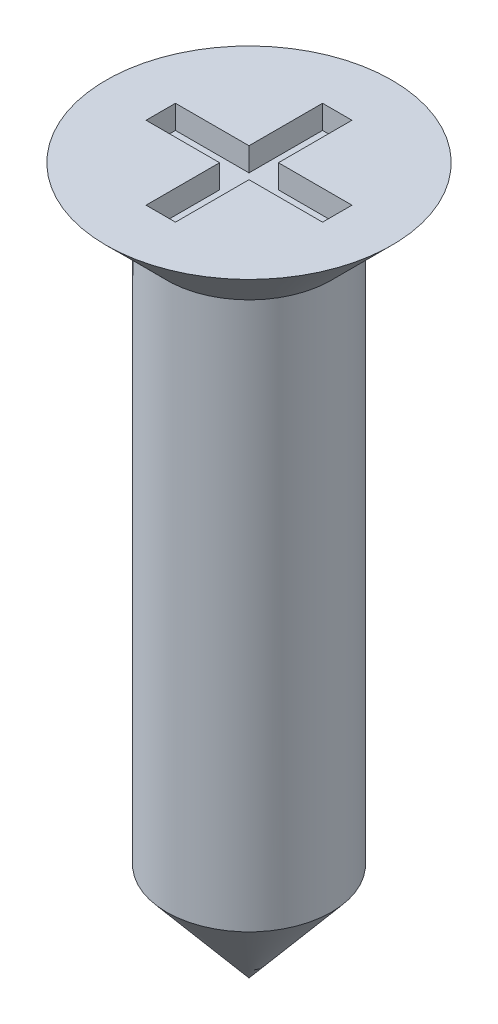
SolidWorks part; units mm, degrees
ref_plane "Front" through (0, 0, 0) normal (0, 0, 1) x (1, 0, 0)
ref_plane "Top" through (0, 0, 0) normal (0, 1, 0) x (1, 0, 0)
ref_plane "Right" through (0, 0, 0) normal (1, 0, 0) x (0, 0, -1)
sketch "Sketch1" plane through (0, 0, 0) normal (0, 0, 1) x (1, 0, 0)
  line L0 (0, 0) -> (-1.215, 0)
  line L1 (-1.215, 0) -> (-0.7, -0.515)
  line L2 (-0.7, -0.515) -> (-0.7, -5.1658)
  line L3 (-0.7, -5.1658) -> (0, -6)
  line L4 (0, -6) -> (0, 0) construction
  line L5 (0, 0) -> (0, -6)
  line L6 (0, -6) -> (-0.7, -6) construction
  dimension "D1" = 2.43
  dimension "D2" = 6
  dimension "D3" = 45
  dimension "D4" = 1.4
  dimension "D5" = 50
revolve "Revolve1" add sketch "Sketch1" angle 360 about L4
sketch "Sketch2" plane through (0, 0, 0) normal (0, 1, 0) x (1, 0, 0)
  line L0 (-0.125, 0.0208) -> (-0.125, 0.125) construction
  line L1 (-0.75, -0.125) -> (-0.125, -0.125)
  line L2 (-0.75, -0.125) -> (-0.75, 0.125)
  line L3 (-0.75, 0.125) -> (-0.125, 0.125)
  line L4 (0.75, -0.125) -> (0.75, 0.125)
  line L5 (-0.75, -0.125) -> (0.75, 0.125) construction
  line L6 (-0.75, 0.125) -> (0.75, -0.125) construction
  line L7 (-0.125, -0.75) -> (0.125, -0.75)
  line L8 (-0.125, -0.75) -> (-0.125, -0.125)
  line L9 (-0.125, 0.75) -> (0.125, 0.75)
  line L10 (0.125, -0.75) -> (0.125, -0.125)
  line L11 (-0.125, -0.75) -> (0, 0) construction
  line L12 (-0.125, 0.75) -> (0.125, -0.75) construction
  line L13 (-0.125, 0.125) -> (-0.125, 0.75)
  line L14 (-0.125, 0.125) -> (-0.0208, 0.125) construction
  line L15 (-0.0208, 0.125) -> (0.0208, 0.125) construction
  line L16 (0.0208, 0.125) -> (0.125, 0.125) construction
  line L17 (0.125, 0.125) -> (0.75, 0.125)
  line L18 (0.125, 0.0208) -> (0.125, 0.125) construction
  line L19 (0.125, 0.125) -> (0.125, 0.75)
  line L20 (0.125, -0.0208) -> (0.125, 0.0208) construction
  line L21 (0.125, -0.125) -> (0.125, -0.0208) construction
  line L22 (0.0208, -0.125) -> (0.125, -0.125) construction
  line L23 (0.125, -0.125) -> (0.75, -0.125)
  line L24 (-0.0208, -0.125) -> (0.0208, -0.125) construction
  line L25 (-0.125, -0.125) -> (-0.0208, -0.125) construction
  line L26 (-0.125, -0.125) -> (-0.125, -0.0208) construction
  line L27 (-0.125, -0.0208) -> (-0.125, 0.0208) construction
  line L28 (0, 0) -> (0.125, 0.75) construction
  point P0 (0, 0)
  point P6 (0, 0)
  dimension "D1" = 0.25
  dimension "D2" = 1.5
extrude "Cut-Extrude1" cut sketch "Sketch2" against normal blind 0.2
